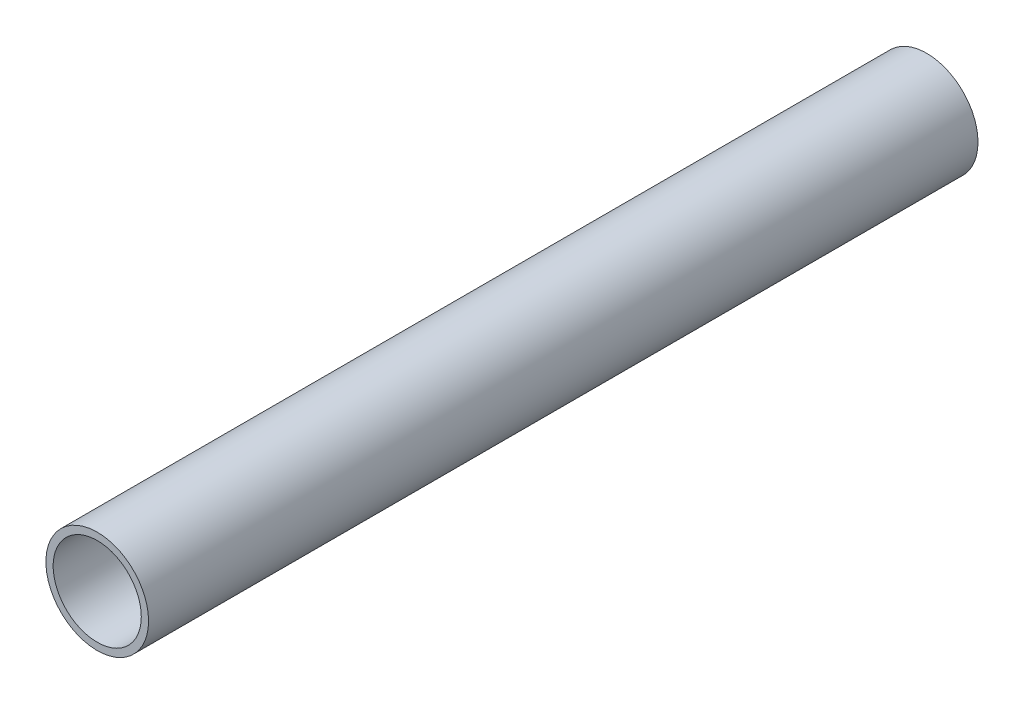
SolidWorks part; units mm, degrees
material "PVC Rigid"
ref_plane "Front Plane" through (0, 0, 0) normal (0, 0, 1) x (1, 0, 0)
ref_plane "Top Plane" through (0, 0, 0) normal (0, 1, 0) x (1, 0, 0)
ref_plane "Right Plane" through (0, 0, 0) normal (1, 0, 0) x (0, 0, -1)
sketch "Sketch1" plane through (0, 0, 0) normal (0, 0, 1) x (1, 0, 0)
  circle A1 centre (0, 0) radius 12.573
  circle A2 centre (0, 0) radius 10.795
  dimension "D1" = 25.146
  dimension "D2" = 21.59
extrude "Boss-Extrude1" add sketch "Sketch1" along normal blind 203.2
